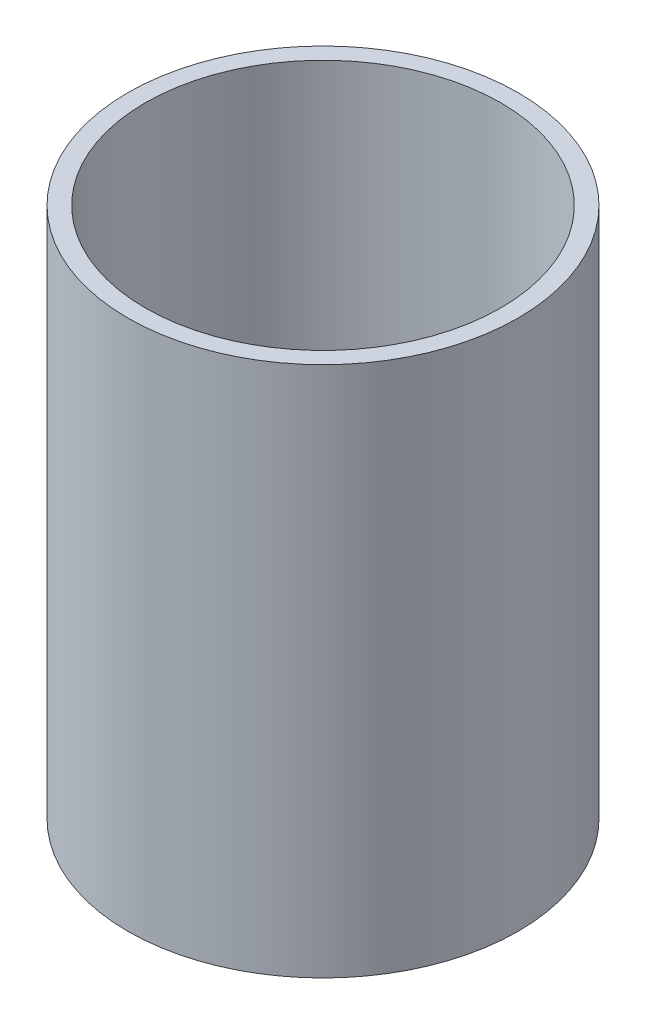
SolidWorks part; units mm, degrees
ref_plane "前视基准面" through (0, 0, 0) normal (0, 0, 1) x (1, 0, 0)
ref_plane "上视基准面" through (0, 0, 0) normal (0, 1, 0) x (1, 0, 0)
ref_plane "右视基准面" through (0, 0, 0) normal (1, 0, 0) x (0, 0, -1)
sketch "草图1" plane through (0, 0, 0) normal (0, 0, 1) x (1, 0, 0)
  line L0 (0, 161.3762) -> (0, 0) construction
  line L1 (141.7365, 0) -> (-131.7984, 0) construction
  line L2 (28, 0) -> (28, 76.2)
  line L3 (25.5, 76.2) -> (28, 76.2)
  line L4 (25.5, 0) -> (28, 0)
  line L7 (25.5, 76.2) -> (25.5, 0)
  dimension "D2" = 28
  dimension "D3" = 76.2
  dimension "D11" = 25.5
revolve "旋转1" add sketch "草图1" angle 360 about L0
cosmetic thread "装饰螺纹线1" parameters "D2"=52
